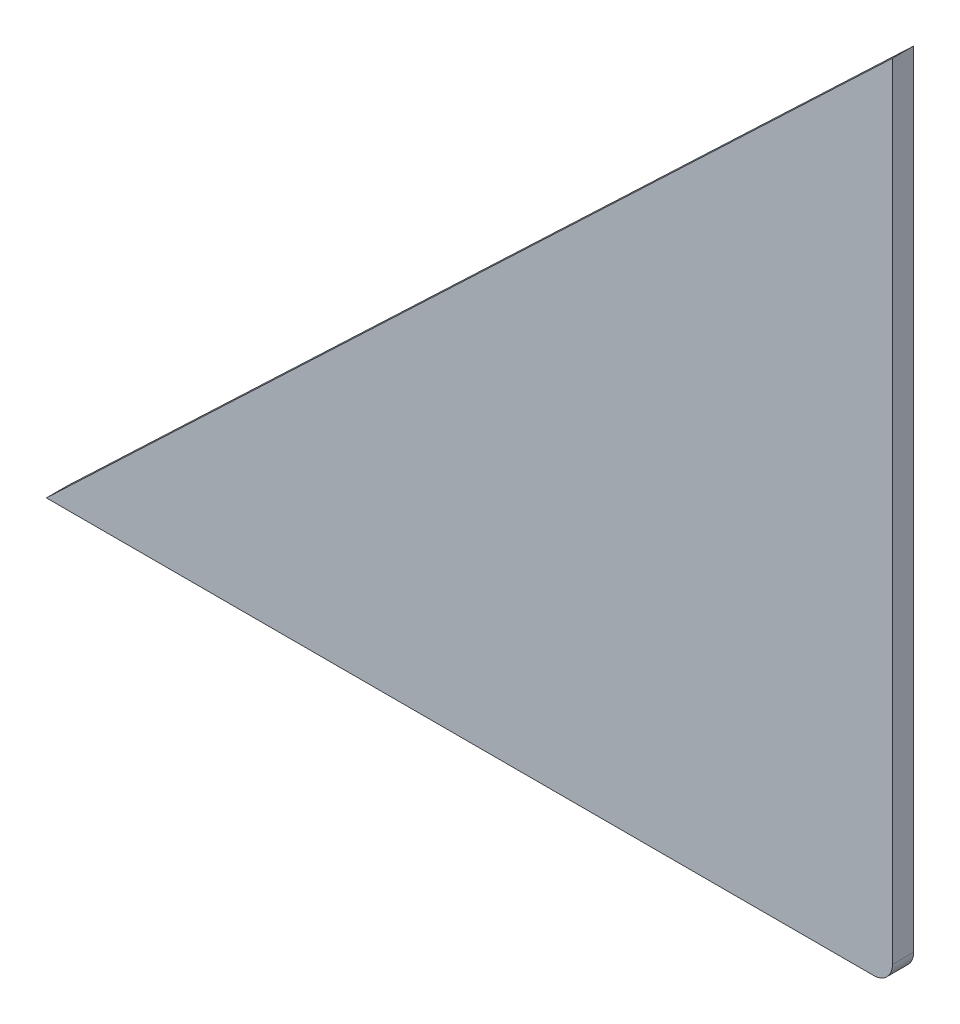
SolidWorks part; units mm, degrees
ref_plane "Front Plane" through (0, 0, 0) normal (0, 0, 1) x (1, 0, 0)
ref_plane "Top Plane" through (0, 0, 0) normal (0, 1, 0) x (1, 0, 0)
ref_plane "Right Plane" through (0, 0, 0) normal (1, 0, 0) x (0, 0, -1)
sketch "Sketch1" plane through (0, 0, 0) normal (0, 0, 1) x (1, 0, 0)
  line L0 (0, 1.8) -> (0, 76)
  line L1 (0, 76) -> (-80, 0)
  line L2 (-80, 0) -> (-1.8, 0)
  arc A0 (0, 1.8) -> (-1.8, 0) centre (-1.8, 1.8) cw
  point P6 (0, 0)
  dimension "D1" = 1.8
  dimension "D2" = 80
  dimension "D3" = 76
extrude "Boss-Extrude1" add sketch "Sketch1" along normal mid plane 2
